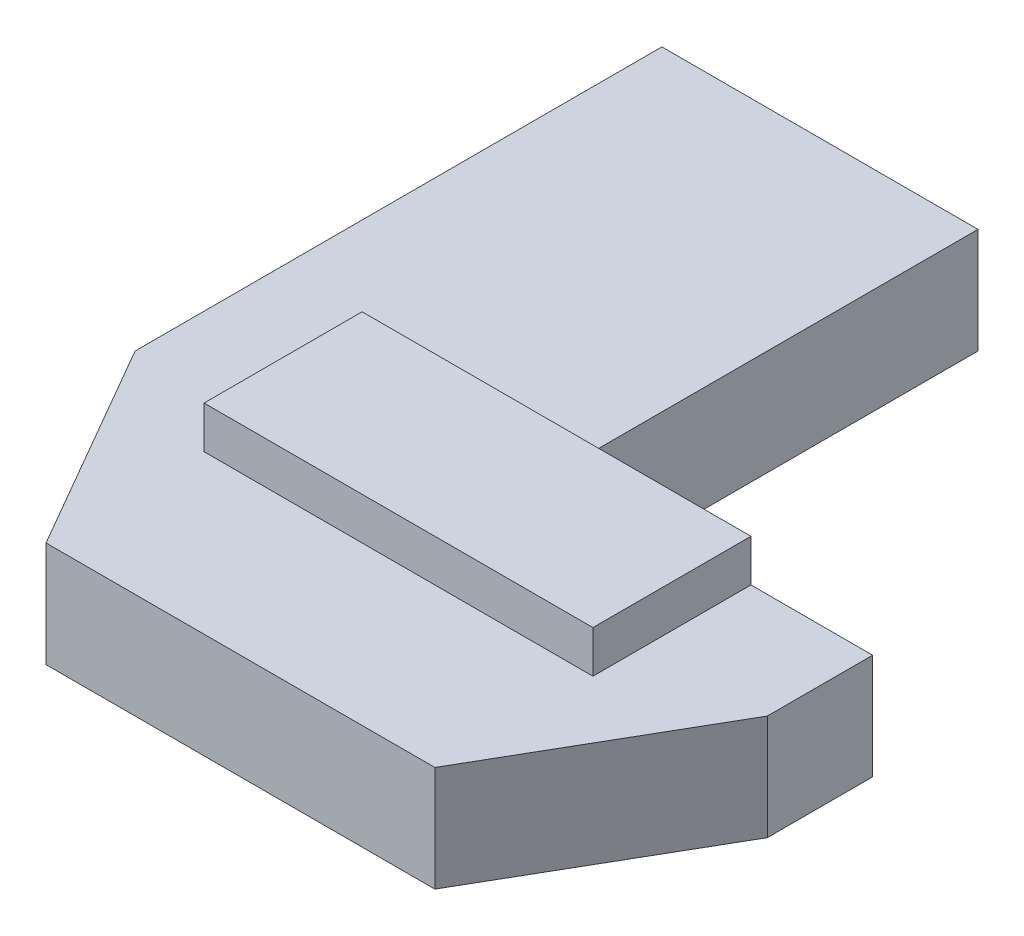
SolidWorks part; units mm, degrees
ref_plane "Ön Düzlem" through (0, 0, 0) normal (0, 0, 1) x (1, 0, 0)
ref_plane "Üst Düzlem" through (0, 0, 0) normal (0, 1, 0) x (1, 0, 0)
ref_plane "Sağ Düzlem" through (0, 0, 0) normal (1, 0, 0) x (0, 0, -1)
sketch "Sketch1" plane through (0, 0, 0) normal (0, 1, 0) x (1, 0, 0)
  line L0 (0, 0) -> (0, 20)
  line L1 (0, 20) -> (-25, 20)
  line L2 (-25, 20) -> (-25, -20)
  line L3 (-25, -20) -> (-8.0005, -49.444)
  line L4 (-8.0005, -49.444) -> (8.0005, -49.444)
  line L5 (8.0005, -49.444) -> (25, -20)
  line L6 (25, -20) -> (25, 0)
  line L7 (25, 0) -> (0, 0)
  dimension "D1" = 25
  dimension "D2" = 40
  dimension "D3" = 60
  dimension "D4" = 60
  dimension "D5" = 25
  dimension "D6" = 20
  dimension "D7" = 20
extrude "Boss-Extrude1" add sketch "Sketch1" along normal blind 5
sketch "Sketch2" plane through (0, 5, 0) normal (0, 1, 0) x (1, 0, 0)
  line L0 (-15, 20) -> (-15, -5)
  line L1 (0, 20) -> (-25, 20) construction
  line L2 (-15, -5) -> (-9.2265, -15)
  line L3 (-9.2265, -15) -> (9.2265, -15)
  line L4 (9.2265, -15) -> (15, -5)
  line L5 (15, -5) -> (15, 0)
  line L6 (25, 0) -> (0, 0) construction
  line L7 (15, 0) -> (25, 0)
  line L8 (25, 0) -> (25, -20)
  line L9 (25, -20) -> (8.0005, -49.444)
  line L10 (8.0005, -49.444) -> (-8.0005, -49.444)
  line L11 (-8.0005, -49.444) -> (-25, -20)
  line L12 (-25, -20) -> (-25, 20)
  line L13 (-25, 20) -> (-15, 20)
  dimension "D1" = 15
  dimension "D2" = 5
  dimension "D3" = 60
  dimension "D4" = 60
  dimension "D5" = 15
  dimension "D6" = 5
  dimension "D7" = 10
extrude "Cut-Extrude1" cut sketch "Sketch2" against normal up to next
sketch "Sketch3" plane through (0, 5, 0) normal (0, 1, 0) x (1, 0, 0)
  line L0 (15, 0) -> (0, 0) construction
  line L1 (9.2265, 0) -> (-9.2265, 0)
  line L2 (9.2265, 0) -> (9.2265, -7.5)
  line L3 (9.2265, -7.5) -> (-9.2265, -7.5)
  line L4 (-9.2265, 0) -> (-9.2265, -7.5)
  dimension "D1" = 0
  dimension "D2" = 0
  dimension "D3" = 7.5
extrude "Boss-Extrude2" add sketch "Sketch3" along normal blind 2
